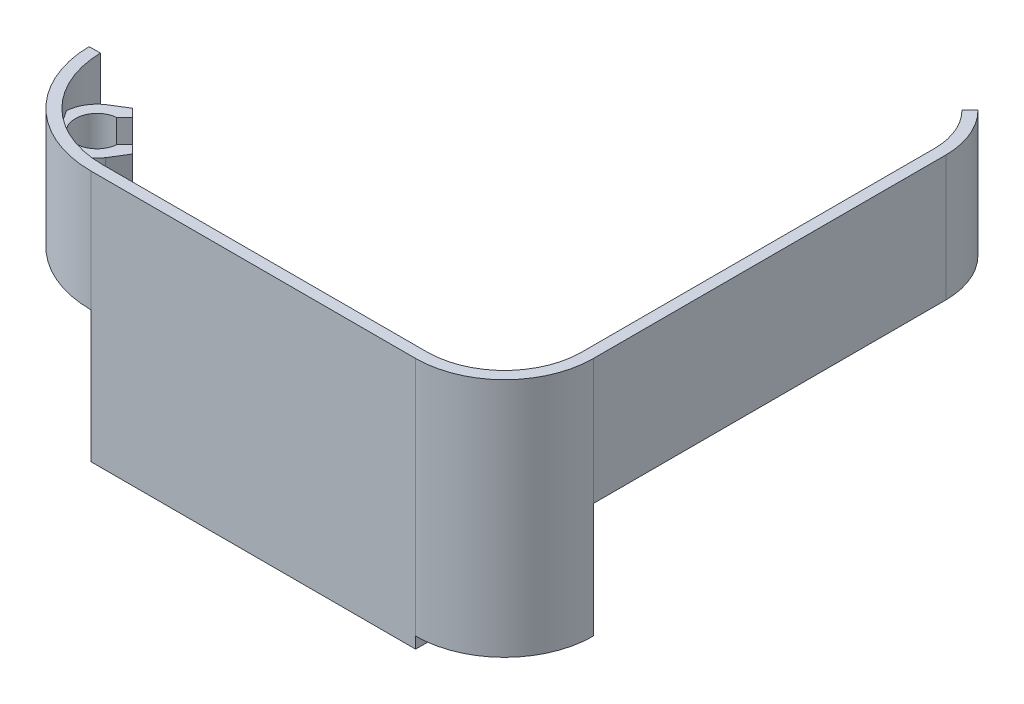
SolidWorks part; units mm, degrees
ref_plane "Front Plane" through (0, 0, 0) normal (0, 0, 1) x (1, 0, 0)
ref_plane "Top Plane" through (0, 0, 0) normal (0, 1, 0) x (1, 0, 0)
ref_plane "Right Plane" through (0, 0, 0) normal (1, 0, 0) x (0, 0, -1)
sketch "Sketch8" plane through (0, 0, 0) normal (0, 1, 0) x (1, 0, 0)
  line L0 (0, -21.844) -> (72.898, -21.844)
  arc A1 (72.898, -21.844) -> (90.3097, -4.4323) centre (72.898, -4.4323) ccw
  arc A3 (0, -21.844) -> (-21.8407, -0.3812) centre (0, 0) cw
  dimension "D1" = 72.898
  dimension "D3" = 21.844
  dimension "D5" = 17.4117
extrude "Extrude-Thin1" add sketch "Sketch8" along normal blind 53.975 thin
sketch "Sketch9" plane through (0, 0, 0) normal (0, 1, 0) x (1, 0, 0)
  line L0 (0, 0) -> (-11.4983, -11.4983) construction
  circle A0 centre (-11.4983, -11.4983) radius 4.6228 construction
  arc A1 (-21.8407, -0.3812) -> (0, -21.844) centre (0, 0) ccw construction
  dimension "D1" = 16.2611
  dimension "D2" = 9.2456
sketch "Sketch10" plane through (0, 0, 0) normal (0, 1, 0) x (1, 0, 0)
  line L4 (0, 0) -> (-20.7337, -20.7337) construction
  line L15 (-6.6412, -11.9364) -> (-4.8435, -10.1387)
  line L16 (-4.8435, -10.1387) -> (-3.0459, -11.9364)
  line L17 (-3.0459, -11.9364) -> (-5.3839, -15.6962)
  line L21 (-11.9364, -3.0459) -> (-15.6962, -5.3839)
  line L22 (-10.1387, -4.8435) -> (-11.9364, -3.0459)
  line L23 (-11.9364, -6.6412) -> (-10.1387, -4.8435)
  arc A2 (-10.9599, -18.8955) -> (-18.8955, -10.9599) centre (0, 0) cw
  circle A3 centre (-11.4983, -11.4983) radius 4.6228 construction
  arc A4 (-11.9364, -6.6412) -> (-6.6412, -11.9364) centre (-11.4983, -11.4983) ccw
  arc A6 (-10.9599, -18.8955) -> (-5.3839, -15.6962) centre (-11.4983, -11.4983) ccw
  arc A7 (-18.8955, -10.9599) -> (-15.6962, -5.3839) centre (-11.4983, -11.4983) cw
  dimension "D1" = 0.254
extrude "Boss-Extrude1" add sketch "Sketch10" along normal blind 19.05 from offset 30.48
sketch "Sketch12" plane through (0, 0, 0) normal (-0.0175, 0, -0.9998) x (-0.9998, 0, 0.0175)
  line L0 (0.3812, 53.975) -> (0.3812, 0) construction
  line L1 (0.3812, 26.9875) -> (35.2486, 26.9875)
  line L2 (0.3812, 26.9875) -> (0.3812, -3.4685)
  line L3 (0.3812, -3.4685) -> (35.2486, -3.4685)
  line L4 (35.2486, 26.9875) -> (35.2486, -3.4685)
  line L5 (0.3812, 53.975) -> (-72.5057, 53.975) construction
  dimension "D1" = 26.9875
extrude "Cut-Extrude1" cut sketch "Sketch12" against normal through all
sketch "Sketch14" plane through (0, 53.975, 0) normal (0, 1, 0) x (1, 0, 0)
  line L0 (85.9457, 85.2116) -> (87.7417, 87.0077)
  line L1 (90.3097, -4.4323) -> (92.8497, -4.4323)
  line L2 (90.3097, -4.4323) -> (90.3097, 74.676)
  line L4 (92.8497, -4.4323) -> (92.8497, 74.676)
  arc A0 (90.3097, 74.676) -> (85.9457, 85.2116) centre (75.4101, 74.676) ccw
  arc A1 (92.8497, 74.676) -> (87.7417, 87.0077) centre (75.4101, 74.676) ccw
  dimension "D3" = 14.8996
  dimension "D4" = 2.54
  dimension "D1" = 79.1083
  dimension "D2" = 2.54
extrude "Boss-Extrude2" add sketch "Sketch14" against normal blind 28.194
sketch "Sketch15" plane through (0, 0, 0) normal (0, -1, 0) x (1, 0, 0)
  line L1 (72.898, 24.384) -> (0, 24.384)
  line L2 (72.898, 24.384) -> (72.898, 18.034)
  line L3 (72.898, 18.034) -> (0, 18.034)
  line L4 (0, 24.384) -> (0, 18.034)
extrude "Boss-Extrude3" add sketch "Sketch15" along normal blind 2.54
equation "\"1.8inin\"=2"
